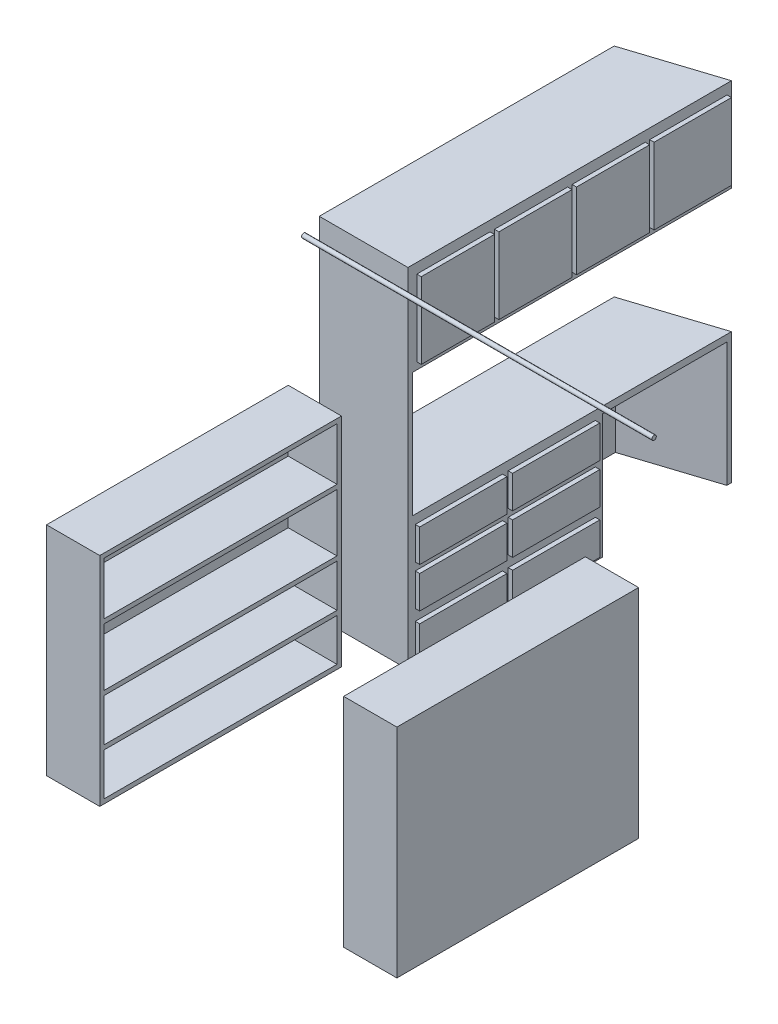
SolidWorks part; units mm, degrees
ref_plane "Front Plane" through (0, 0, 0) normal (0, 0, 1) x (1, 0, 0)
ref_plane "Top Plane" through (0, 0, 0) normal (0, 1, 0) x (1, 0, 0)
ref_plane "Right Plane" through (0, 0, 0) normal (1, 0, 0) x (0, 0, -1)
sketch "Sketch12" plane through (0, 0, 0) normal (0, 1, 0) x (1, 0, 0)
  line L0 (0, 0) -> (0, 2073.1148) construction
ref_plane "Plane1" through (0, 0, 0) normal (1, 0, 0) x (0, 0, -1)
sketch "Sketch1" plane through (1003.3, 0, 0) normal (-1, 0, 0) x (0, 0, 1)
  line L0 (0, 0) -> (0, 1943.1) construction
  line L1 (1778, 2019.3) -> (-1778, 2019.3) construction
  circle A0 centre (0, 1943.1) radius 12.7
  dimension "D1" = 76.2
extrude "Boss-Extrude1" add sketch "Sketch1" along normal up to surface (2006.6 mm away)
sketch3d "3DSketch1" plane through (0, 0, 0) normal (0, 0, 1) x (1, 0, 0)
  dimension "D1" = 711.2
sketch "Sketch3" plane through (0, 711.2, 0) normal (0, 1, 0) x (1, 0, 0)
  line L0 (0, 2101.2892) -> (-1003.3, 1778) construction
  line L1 (-1003.3, 1778) -> (-1003.3, -1778) construction
  line L2 (-495.3, 1941.6907) -> (-1003.3, 1778)
  line L3 (-1003.3, 1778) -> (-1003.3, 88.9)
  line L4 (-1003.3, 88.9) -> (-495.3, 88.9)
  line L5 (-495.3, 88.9) -> (-495.3, 1941.6907)
  line L6 (1003.3, 12.7) -> (-1003.3, 12.7) construction
  dimension "D1" = 76.2
  dimension "D2" = 508
extrude "Boss-Extrude2" add sketch "Sketch3" along normal blind 38.1 separate body
sketch "Sketch4" plane through (0, 711.2, 0) normal (0, -1, 0) x (1, 0, 0)
  line L0 (-520.7, -114.3) -> (-977.9, -114.3)
  line L1 (-977.9, -114.3) -> (-977.9, -1178.4047)
  line L2 (-977.9, -1759.4985) -> (-520.7, -1906.8201)
  line L3 (-977.9, -1759.4985) -> (-487.5099, -1917.5148) construction
  line L4 (-1003.3, -88.9) -> (-1003.3, -1778)
  line L5 (-1003.3, -1778) -> (-495.3, -1941.6907)
  line L6 (-495.3, -1941.6907) -> (-495.3, -88.9)
  line L7 (-495.3, -88.9) -> (-1003.3, -88.9)
  line L8 (-1003.3, -88.9) -> (-1003.3, -1778)
  line L9 (-1003.3, -1778) -> (-495.3, -1941.6907)
  line L10 (-495.3, -1941.6907) -> (-495.3, -1915.0047)
  line L11 (-495.3, -88.9) -> (-1003.3, -88.9)
  line L12 (-520.7, -1203.8047) -> (-977.9, -1203.8047)
  line L13 (-520.7, -1178.4047) -> (-977.9, -1178.4047)
  line L16 (-495.3, -114.3) -> (-977.9, -114.3) construction
  line L17 (-495.3, -1203.8047) -> (-977.9, -1203.8047) construction
  line L18 (-520.7, -1178.4047) -> (-520.7, -114.3)
  line L19 (-495.3, -1178.4047) -> (-977.9, -1178.4047) construction
  line L20 (-977.9, -1203.8047) -> (-977.9, -1759.4985)
  line L21 (-977.9, -114.3) -> (-977.9, -1759.4985) construction
  line L22 (-520.7, -1203.8047) -> (-495.3, -1203.8047)
  line L23 (-520.7, -1906.8201) -> (-495.3, -1915.0047)
  line L24 (-495.3, -1203.8047) -> (-495.3, -88.9)
  dimension "D3" = 555.6938
  dimension "D1" = 0
  dimension "D2" = 25.4
  dimension "D4" = 25.4
extrude "Boss-Extrude3" add sketch "Sketch4" along normal up to surface (711.2 mm away)
sketch "Sketch5" plane through (-495.3, 0, 0) normal (1, 0, 0) x (0, 0, -1)
  line L0 (646.3523, 0) -> (646.3523, 749.3) construction
  line L1 (1203.8047, 0) -> (88.9, 0) construction
  line L2 (88.9, 749.3) -> (1941.6907, 749.3) construction
  line L3 (88.9, 249.7667) -> (1203.8047, 249.7667) construction
  line L4 (88.9, 749.3) -> (88.9, 0) construction
  line L5 (1203.8047, 0) -> (1203.8047, 711.2) construction
  line L6 (88.9, 499.5333) -> (1203.8047, 499.5333) construction
  line L7 (114.3, 711.2) -> (646.3523, 499.5333) construction
  line L8 (646.3523, 499.5333) -> (1178.4047, 249.7667) construction
  line L9 (1178.4047, 0) -> (1178.4047, 711.2) construction
  line L10 (1178.4047, 249.7667) -> (646.3523, 0) construction
  line L11 (646.3523, 0) -> (114.3, 249.7667) construction
  line L12 (1162.0228, 698.5) -> (662.7342, 698.5)
  line L13 (114.3, 249.7667) -> (646.3523, 499.5333) construction
  line L14 (646.3523, 499.5333) -> (1178.4047, 711.2) construction
  line L15 (114.3, 0) -> (114.3, 711.2) construction
  line L16 (662.7342, 512.2333) -> (662.7342, 698.5)
  line L17 (130.6819, 512.2333) -> (629.9704, 512.2333)
  line L18 (130.6819, 512.2333) -> (130.6819, 698.5)
  line L19 (130.6819, 698.5) -> (629.9704, 698.5)
  line L20 (629.9704, 512.2333) -> (629.9704, 698.5)
  line L21 (130.6819, 512.2333) -> (629.9704, 698.5) construction
  line L22 (130.6819, 698.5) -> (629.9704, 512.2333) construction
  line L23 (1162.0228, 512.2333) -> (662.7342, 512.2333)
  line L24 (1162.0228, 512.2333) -> (1162.0228, 698.5)
  line L25 (662.7342, 217.9743) -> (1162.0228, 217.9743)
  line L26 (629.9704, 281.559) -> (130.6819, 281.559)
  line L27 (629.9704, 281.559) -> (629.9704, 467.741)
  line L28 (629.9704, 467.741) -> (130.6819, 467.741)
  line L29 (130.6819, 281.559) -> (130.6819, 467.741)
  line L30 (629.9704, 281.559) -> (130.6819, 467.741) construction
  line L31 (629.9704, 467.741) -> (130.6819, 281.559) construction
  line L32 (629.9704, 31.7923) -> (130.6819, 31.7923)
  line L33 (629.9704, 31.7923) -> (629.9704, 217.9743)
  line L34 (629.9704, 217.9743) -> (130.6819, 217.9743)
  line L35 (130.6819, 31.7923) -> (130.6819, 217.9743)
  line L36 (629.9704, 31.7923) -> (130.6819, 217.9743) construction
  line L37 (629.9704, 217.9743) -> (130.6819, 31.7923) construction
  line L38 (1162.0228, 31.7923) -> (1162.0228, 217.9743)
  line L39 (662.7342, 31.7923) -> (1162.0228, 31.7923)
  line L40 (662.7342, 31.7923) -> (662.7342, 217.9743)
  line L41 (662.7342, 467.741) -> (1162.0228, 467.741)
  line L42 (1162.0228, 281.559) -> (1162.0228, 467.741)
  line L43 (662.7342, 281.559) -> (1162.0228, 281.559)
  line L44 (662.7342, 281.559) -> (662.7342, 467.741)
  point P28 (380.3262, 605.3667)
  point P34 (380.3262, 374.65)
  point P39 (380.3262, 124.8833)
  dimension "D1" = 249.7667
  dimension "D2" = 249.7667
  dimension "D3" = 12.7
  dimension "D4" = 16.3819
  dimension "D5" = 186.182
  dimension "D6" = 186.182
extrude "Boss-Extrude4" add sketch "Sketch5" along normal blind 25.4
sketch "Sketch6" plane through (0, 749.3, 0) normal (0, 1, 0) x (1, 0, 0)
  line L0 (-495.3, 88.9) -> (-495.3, 1941.6907) construction
  line L1 (-1003.3, 88.9) -> (-495.3, 88.9)
  line L2 (-1003.3, 88.9) -> (-1003.3, 114.3)
  line L3 (-1003.3, 114.3) -> (-495.3, 114.3)
  line L4 (-495.3, 88.9) -> (-495.3, 114.3)
  line L5 (-520.7, 114.3) -> (-977.9, 114.3) construction
extrude "Boss-Extrude5" add sketch "Sketch6" along normal offset from surface (1244.6 mm away) 25.4
sketch "Sketch7" plane through (0, 0, -114.3) normal (0, 0, -1) x (-1, 0, 0)
  line L0 (1003.3, 2019.3) -> (1003.3, 0) construction
  line L1 (495.3, 1993.9) -> (1003.3, 1993.9)
  line L2 (495.3, 1993.9) -> (495.3, 1460.5)
  line L3 (495.3, 1460.5) -> (1003.3, 1460.5)
  line L4 (1003.3, 1993.9) -> (1003.3, 1460.5)
  line L5 (495.3, 749.3) -> (1003.3, 749.3) construction
  line L6 (520.7, 1968.5) -> (520.7, 1485.9)
  line L7 (520.7, 1485.9) -> (977.9, 1485.9)
  line L8 (977.9, 1968.5) -> (977.9, 1485.9)
  line L9 (520.7, 1968.5) -> (977.9, 1968.5)
  dimension "D1" = 711.2
  dimension "D2" = 25.4
extrude "Boss-Extrude6" add sketch "Sketch7" along normal up to surface (1663.7 mm away)
sketch "Sketch8" plane through (-495.3, 0, 0) normal (1, 0, 0) x (0, 0, -1)
  line L0 (114.3, 1968.5) -> (114.3, 1485.9) construction
  line L1 (139.7, 1935.7327) -> (558.8, 1935.7327)
  line L2 (139.7, 1935.7327) -> (139.7, 1500.3079)
  line L3 (139.7, 1500.3079) -> (558.8, 1500.3079)
  line L4 (558.8, 1935.7327) -> (558.8, 1500.3079)
  line L5 (584.2, 1935.7327) -> (1003.3, 1935.7327)
  line L6 (584.2, 1935.7327) -> (584.2, 1500.3079)
  line L7 (584.2, 1500.3079) -> (1003.3, 1500.3079)
  line L8 (1003.3, 1935.7327) -> (1003.3, 1500.3079)
  line L9 (1028.7, 1935.7327) -> (1447.8, 1935.7327)
  line L10 (1028.7, 1935.7327) -> (1028.7, 1500.3079)
  line L11 (1028.7, 1500.3079) -> (1447.8, 1500.3079)
  line L12 (1447.8, 1935.7327) -> (1447.8, 1500.3079)
  line L13 (1473.2, 1935.7327) -> (1916.2907, 1935.7327)
  line L14 (1473.2, 1935.7327) -> (1473.2, 1500.3079)
  line L15 (1473.2, 1500.3079) -> (1916.2907, 1500.3079)
  line L16 (1916.2907, 1935.7327) -> (1916.2907, 1500.3079)
  line L17 (1941.6907, 1460.5) -> (1941.6907, 1993.9) construction
  line L18 (114.3, 1727.2) -> (1916.2907, 1727.2) construction
  dimension "D1" = 25.4
  dimension "D2" = 25.4
  dimension "D3" = 25.4
  dimension "D4" = 25.4
  dimension "D5" = 25.4
  dimension "D6" = 419.1
  dimension "D7" = 419.1
  dimension "D8" = 419.1
extrude "Boss-Extrude7" add sketch "Sketch8" along normal blind 25.4
sketch "Sketch9" plane through (0, 0, 0) normal (0, 1, 0) x (1, 0, 0)
  line L0 (-1003.3, 1778) -> (-1003.3, -1778) construction
  line L1 (-1003.3, -1473.2) -> (-698.5, -1473.2)
  line L2 (-1003.3, -1473.2) -> (-1003.3, -88.9)
  line L3 (-1003.3, -88.9) -> (-698.5, -88.9)
  line L4 (-698.5, -1473.2) -> (-698.5, -88.9)
  line L5 (-1003.3, -1778) -> (1003.3, -1778) construction
  line L6 (-1003.3, -12.7) -> (1003.3, -12.7) construction
  dimension "D1" = 304.8
  dimension "D2" = 76.2
  dimension "D3" = 304.8
extrude "Boss-Extrude8" add sketch "Sketch9" along normal blind 25.4 separate body
sketch "Sketch10" plane through (0, 25.4, 0) normal (0, 1, 0) x (1, 0, 0)
  line L0 (-698.5, -114.3) -> (-977.9, -114.3)
  line L1 (-977.9, -114.3) -> (-977.9, -1447.8)
  line L2 (-977.9, -1447.8) -> (-698.5, -1447.8)
  line L3 (-698.5, -114.3) -> (-698.5, -88.9)
  line L4 (-1003.3, -88.9) -> (-1003.3, -1473.2)
  line L5 (-1003.3, -1473.2) -> (-698.5, -1473.2)
  line L6 (-698.5, -1473.2) -> (-698.5, -88.9)
  line L7 (-698.5, -88.9) -> (-1003.3, -88.9)
  line L8 (-1003.3, -88.9) -> (-1003.3, -1473.2)
  line L9 (-1003.3, -1473.2) -> (-698.5, -1473.2)
  line L10 (-698.5, -1473.2) -> (-698.5, -1447.8)
  line L11 (-698.5, -88.9) -> (-1003.3, -88.9)
  dimension "D1" = 0
  dimension "D2" = 25.4
extrude "Boss-Extrude9" add sketch "Sketch10" along normal blind 1219.2
sketch "Sketch11" plane through (-977.9, 0, 0) normal (1, 0, 0) x (0, 0, -1)
  line L0 (-88.9, 1244.6) -> (-88.9, 0) construction
  line L1 (-1473.2, 1244.6) -> (-88.9, 1244.6)
  line L2 (-1473.2, 1244.6) -> (-1473.2, 1219.2)
  line L3 (-1473.2, 1219.2) -> (-88.9, 1219.2)
  line L4 (-88.9, 1244.6) -> (-88.9, 1219.2)
  line L5 (-1473.2, 1244.6) -> (-1473.2, 0) construction
  line L6 (-1473.2, 918.4161) -> (-88.9, 918.4161)
  line L7 (-1473.2, 918.4161) -> (-1473.2, 893.0161)
  line L8 (-1473.2, 893.0161) -> (-88.9, 893.0161)
  line L9 (-88.9, 918.4161) -> (-88.9, 893.0161)
  line L11 (-1473.2, 563.1407) -> (-88.9, 563.1407)
  line L12 (-1473.2, 563.1407) -> (-1473.2, 537.7407)
  line L13 (-1473.2, 537.7407) -> (-88.9, 537.7407)
  line L14 (-88.9, 563.1407) -> (-88.9, 537.7407)
  line L15 (-1473.2, 293.3918) -> (-88.9, 293.3918)
  line L16 (-1473.2, 293.3918) -> (-1473.2, 267.9918)
  line L17 (-1473.2, 267.9918) -> (-88.9, 267.9918)
  line L18 (-88.9, 293.3918) -> (-88.9, 267.9918)
  dimension "D1" = 25.4
  dimension "D2" = 25.4
  dimension "D3" = 25.4
  dimension "D4" = 25.4
extrude "Boss-Extrude10" add sketch "Sketch11" along normal up to surface (279.4 mm away) up to face at (-698.5, 628.65, 781.05)
mirror "Mirror1" about plane through (0, 0, 0) normal (1, 0, 0) of bodies 110
